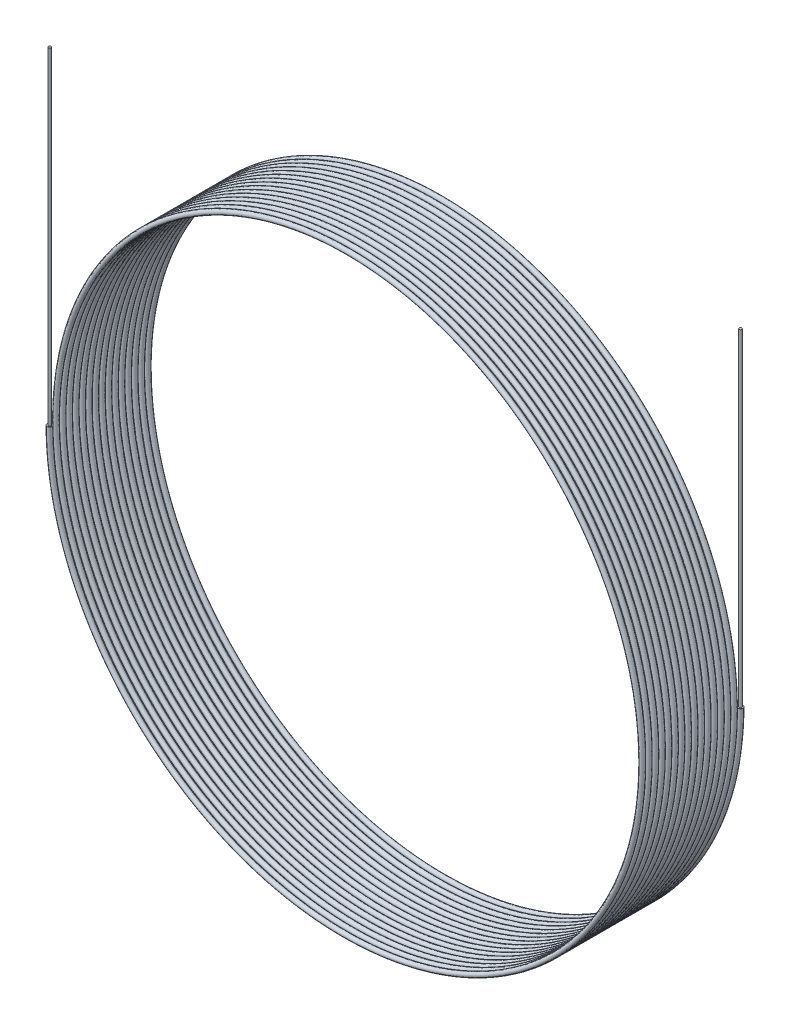
SolidWorks part; units mm, degrees
ref_plane "Front Plane" through (0, 0, 0) normal (0, 0, 1) x (1, 0, 0)
ref_plane "Top Plane" through (0, 0, 0) normal (0, 1, 0) x (1, 0, 0)
ref_plane "Right Plane" through (0, 0, 0) normal (1, 0, 0) x (0, 0, -1)
sketch "Sketch1" plane through (0, 0, 0) normal (0, 0, 1) x (1, 0, 0)
  circle A0 centre (0, 0) radius 90
  dimension "D1" = 180
curve "Helix/Spiral1" pitch 2 height 31 turns 15.5
sketch "Sketch2" plane through (0, 0, 0) normal (0, 1, 0) x (1, 0, 0)
  circle A0 centre (90, 0) radius 0.75
  spline S0 degree 3 poles (90, 0) (90, -0.0158) (89.3294, -0.0476) (86.3342, -0.0951) (81.4162, -0.1426) (74.6852, -0.1902) (66.2909, -0.2377) (56.4203, -0.2853) (45.2932, -0.3328) (33.1575, -0.3804) (20.2833, -0.4279) (6.9574, -0.4755) (-6.5234, -0.523) (-19.8589, -0.5706) (-32.7522, -0.6181) (-44.9161, -0.6656) (-56.0797, -0.7132) (-65.9944, -0.7607) (-74.4395, -0.8083) (-81.2267, -0.8558) (-86.2051, -0.9034) (-89.2636, -0.9509) (-90.3342, -0.9985) (-89.3931, -1.046) (-86.4613, -1.0936) (-81.6039, -1.1411) (-74.9292, -1.1887) (-66.5858, -1.2362) (-56.7596, -1.2837) (-45.6693, -1.3313) (-33.562, -1.3788) (-20.7072, -1.4264) (-7.3913, -1.4739) (6.0892, -1.5215) (19.4341, -1.569) (32.3462, -1.6166) (44.5379, -1.6641) (55.7378, -1.7117) (65.6964, -1.7592) (74.192, -1.8067) (81.0353, -1.8543) (86.0739, -1.9018) (89.1957, -1.9494) (90.3311, -1.9969) (89.4548, -2.0445) (86.5864, -2.092) (81.7896, -2.1396) (75.1715, -2.1871) (66.8792, -2.2347) (57.0976, -2.2822) (46.0443, -2.3298) (33.9657, -2.3773) (21.1307, -2.4248) (7.8251, -2.4724) (-5.6548, -2.5199) (-19.0088, -2.5675) (-31.9394, -2.615) (-44.1587, -2.6626) (-55.3946, -2.7101) (-65.3969, -2.7577) (-73.9428, -2.8052) (-80.842, -2.8528) (-85.9408, -2.9003) (-89.1258, -2.9479) (-90.3259, -2.9954) (-89.5144, -3.0429) (-86.7095, -3.0905) (-81.9735, -3.138) (-75.412, -3.1856) (-67.171, -3.2331) (-57.4342, -3.2807) (-46.4183, -3.3282) (-34.3687, -3.3758) (-21.5536, -3.4233) (-8.2586, -3.4709) (5.2203, -3.5184) (18.583, -3.566) (31.5319, -3.6135) (43.7785, -3.661) (55.0502, -3.7086) (65.0959, -3.7561) (73.6919, -3.8037) (80.6468, -3.8512) (85.8057, -3.8988) (89.0537, -3.9463) (90.3185, -3.9939) (89.5719, -4.0414) (86.8305, -4.089) (82.1554, -4.1365) (75.6507, -4.184) (67.4613, -4.2316) (57.7695, -4.2791) (46.7912, -4.3267) (34.7708, -4.3742) (21.9761, -4.4218) (8.692, -4.4693) (-4.7857, -4.5169) (-18.1569, -4.5644) (-31.1236, -4.612) (-43.3973, -4.6595) (-54.7044, -4.7071) (-64.7933, -4.7546) (-73.4393, -4.8021) (-80.4498, -4.8497) (-85.6686, -4.8972) (-88.9796, -4.9448) (-90.3091, -4.9923) (-89.6273, -5.0399) (-86.9496, -5.0874) (-82.3355, -5.135) (-75.8877, -5.1825) (-67.75, -5.2301) (-58.1034, -5.2776) (-47.1629, -5.3252) (-35.1721, -5.3727) (-22.398, -5.4202) (-9.1251, -5.4678) (4.351, -5.5153) (17.7303, -5.5629) (30.7146, -5.6104) (43.015, -5.658) (54.3574, -5.7055) (64.4893, -5.7531) (73.185, -5.8006) (80.2509, -5.8482) (85.5295, -5.8957) (88.9035, -5.9433) (90.2975, -5.9908) (89.6807, -6.0383) (87.0666, -6.0859) (82.5136, -6.1334) (76.123, -6.181) (68.0371, -6.2285) (58.4361, -6.2761) (47.5336, -6.3236) (35.5726, -6.3712) (22.8194, -6.4187) (9.558, -6.4663) (-3.9162, -6.5138) (-17.3032, -6.5613) (-30.3049, -6.6089) (-42.6317, -6.6564) (-54.0091, -6.704) (-64.1837, -6.7515) (-72.929, -6.7991) (-80.0501, -6.8466) (-85.3885, -6.8942) (-88.8253, -6.9417) (-90.2839, -6.9893) (-89.7319, -7.0368) (-87.1816, -7.0844) (-82.6898, -7.1319) (-76.3565, -7.1794) (-68.3227, -7.227) (-58.7673, -7.2745) (-47.9032, -7.3221) (-35.9723, -7.3696) (-23.2403, -7.4172) (-9.9908, -7.4647) (3.4813, -7.5123) (16.8758, -7.5598) (29.8945, -7.6074) (42.2475, -7.6549) (53.6596, -7.7025) (63.8767, -7.75) (72.6713, -7.7975) (79.8474, -7.8451) (85.2454, -7.8926) (88.745, -7.9402) (90.2682, -7.9877) (89.7811, -8.0353) (87.2946, -8.0828) (82.8641, -8.1304) (76.5882, -8.1779) (68.6066, -8.2255) (59.0972, -8.273) (48.2717, -8.3206) (36.3712, -8.3681) (23.6607, -8.4156) (10.4232, -8.4632) (-3.0463, -8.5107) (-16.448, -8.5583) (-29.4834, -8.6058) (-41.8623, -8.6534) (-53.3088, -8.7009) (-63.5682, -8.7485) (-72.4119, -8.796) (-79.643, -8.8436) (-85.1004, -8.8911) (-88.6626, -8.9387) (-90.2504, -8.9862) (-89.8282, -9.0337) (-87.4056, -9.0813) (-83.0365, -9.1288) (-76.8181, -9.1764) (-68.889, -9.2239) (-59.4257, -9.2715) (-48.639, -9.319) (-36.7692, -9.3666) (-24.0805, -9.4141) (-10.8555, -9.4617) (2.6113, -9.5092) (16.0198, -9.5567) (29.0717, -9.6043) (41.4761, -9.6518) (52.9568, -9.6994) (63.2582, -9.7469) (72.1508, -9.7945) (79.4366, -9.842) (84.9534, -9.8896) (88.5782, -9.9371) (90.2304, -9.9847) (89.8732, -10.0322) (87.5145, -10.0798) (83.2069, -10.1273) (77.0462, -10.1748) (69.1698, -10.2224) (59.7529, -10.2699) (49.0053, -10.3175) (37.1663, -10.365) (24.4997, -10.4126) (11.2875, -10.4601) (-2.1761, -10.5077) (-15.5913, -10.5552) (-28.6592, -10.6028) (-41.0889, -10.6503) (-52.6036, -10.6979) (-62.9467, -10.7454) (-71.888, -10.7929) (-79.2284, -10.8405) (-84.8044, -10.888) (-88.4918, -10.9356) (-90.2084, -10.9831) (-89.9162, -11.0307) (-87.6214, -11.0782) (-83.3754, -11.1258) (-77.2726, -11.1733) (-69.4489, -11.2209) (-60.0786, -11.2684) (-49.3704, -11.316) (-37.5626, -11.3635) (-24.9184, -11.411) (-11.7192, -11.4586) (1.741, -11.5061) (15.1624, -11.5537) (28.2461, -11.6012) (40.7008, -11.6488) (52.2491, -11.6963) (62.6338, -11.7439) (71.6236, -11.7914) (79.0184, -11.839) (84.6534, -11.8865) (88.4033, -11.934) (90.1843, -11.9816) (89.957, -12.0291) (87.7263, -12.0767) (83.542, -12.1242) (77.4971, -12.1718) (69.7265, -12.2193) (60.403, -12.2669) (49.7343, -12.3144) (37.958, -12.362) (25.3365, -12.4095) (12.1506, -12.4571) (-1.3058, -12.5046) (-14.7331, -12.5521) (-27.8323, -12.5997) (-40.3117, -12.6472) (-51.8934, -12.6948) (-62.3194, -12.7423) (-71.3575, -12.7899) (-78.8065, -12.8374) (-84.5005, -12.885) (-88.3127, -12.9325) (-90.1581, -12.9801) (-89.9957, -13.0276) (-87.8292, -13.0752) (-83.7066, -13.1227) (-77.7199, -13.1702) (-70.0024, -13.2178) (-60.7259, -13.2653) (-50.0971, -13.3129) (-38.3526, -13.3604) (-25.754, -13.408) (-12.5818, -13.4555) (0.8705, -13.5031) (14.3035, -13.5506) (27.4179, -13.5982) (39.9217, -13.6457) (51.5365, -13.6933) (62.0036, -13.7408) (71.0898, -13.7883) (78.5929, -13.8359) (84.3457, -13.8834) (88.2201, -13.931) (90.1298, -13.9785) (90.0324, -14.0261) (87.9299, -14.0736) (83.8693, -14.1212) (77.9409, -14.1687) (70.2767, -14.2163) (61.0475, -14.2638) (50.4587, -14.3113) (38.7462, -14.3589) (26.1709, -14.4064) (13.0127, -14.454) (-0.4353, -14.5015) (-13.8735, -14.5491) (-27.0029, -14.5966) (-39.5308, -14.6442) (-51.1784, -14.6917) (-61.6863, -14.7393) (-70.8204, -14.7868) (-78.3773, -14.8344) (-84.1888, -14.8819) (-88.1254, -14.9294) (-90.0995, -14.977) (-90.067, -15.0245) (-88.0287, -15.0721) (-84.03, -15.1196) (-78.16, -15.1672) (-70.5494, -15.2147) (-61.3676, -15.2623) (-50.8192, -15.3098) (-39.139, -15.3574) (-26.5872, -15.4049) (-9.062, -15.4683) (9.062, -15.5317) (26.5872, -15.5951) (39.139, -15.6426) (50.8192, -15.6902) (61.3676, -15.7377) (70.5494, -15.7853) (78.16, -15.8328) (84.03, -15.8804) (88.0287, -15.9279) (90.067, -15.9755) (90.0995, -16.023) (88.1254, -16.0706) (84.1888, -16.1181) (78.3773, -16.1656) (70.8204, -16.2132) (61.6863, -16.2607) (51.1784, -16.3083) (39.5308, -16.3558) (27.0029, -16.4034) (13.8735, -16.4509) (0.4353, -16.4985) (-13.0127, -16.546) (-26.1709, -16.5936) (-38.7462, -16.6411) (-50.4587, -16.6887) (-61.0475, -16.7362) (-70.2767, -16.7837) (-77.9409, -16.8313) (-83.8693, -16.8788) (-87.9299, -16.9264) (-90.0324, -16.9739) (-90.1298, -17.0215) (-88.2201, -17.069) (-84.3457, -17.1166) (-78.5929, -17.1641) (-71.0898, -17.2117) (-62.0036, -17.2592) (-51.5365, -17.3067) (-39.9217, -17.3543) (-27.4179, -17.4018) (-14.3035, -17.4494) (-0.8705, -17.4969) (12.5818, -17.5445) (25.754, -17.592) (38.3526, -17.6396) (50.0971, -17.6871) (60.7259, -17.7347) (70.0024, -17.7822) (77.7199, -17.8298) (83.7066, -17.8773) (87.8292, -17.9248) (89.9957, -17.9724) (90.1581, -18.0199) (88.3127, -18.0675) (84.5005, -18.115) (78.8065, -18.1626) (71.3575, -18.2101) (62.3194, -18.2577) (51.8934, -18.3052) (40.3117, -18.3528) (27.8323, -18.4003) (14.7331, -18.4479) (1.3058, -18.4954) (-12.1506, -18.5429) (-25.3365, -18.5905) (-37.958, -18.638) (-49.7343, -18.6856) (-60.403, -18.7331) (-69.7265, -18.7807) (-77.4971, -18.8282) (-83.542, -18.8758) (-87.7263, -18.9233) (-89.957, -18.9709) (-90.1843, -19.0184) (-88.4033, -19.066) (-84.6534, -19.1135) (-79.0184, -19.161) (-71.6236, -19.2086) (-62.6338, -19.2561) (-52.2491, -19.3037) (-40.7008, -19.3512) (-28.2461, -19.3988) (-15.1624, -19.4463) (-1.741, -19.4939) (11.7192, -19.5414) (24.9184, -19.589) (37.5626, -19.6365) (49.3704, -19.684) (60.0786, -19.7316) (69.4489, -19.7791) (77.2726, -19.8267) (83.3754, -19.8742) (87.6214, -19.9218) (89.9162, -19.9693) (90.2084, -20.0169) (88.4918, -20.0644) (84.8044, -20.112) (79.2284, -20.1595) (71.888, -20.2071) (62.9467, -20.2546) (52.6036, -20.3021) (41.0889, -20.3497) (28.6592, -20.3972) (15.5913, -20.4448) (2.1761, -20.4923) (-11.2875, -20.5399) (-24.4997, -20.5874) (-37.1663, -20.635) (-49.0053, -20.6825) (-59.7529, -20.7301) (-69.1698, -20.7776) (-77.0462, -20.8252) (-83.2069, -20.8727) (-87.5145, -20.9202) (-89.8732, -20.9678) (-90.2304, -21.0153) (-88.5782, -21.0629) (-84.9534, -21.1104) (-79.4366, -21.158) (-72.1508, -21.2055) (-63.2582, -21.2531) (-52.9568, -21.3006) (-41.4761, -21.3482) (-29.0717, -21.3957) (-16.0198, -21.4433) (-2.6113, -21.4908) (10.8555, -21.5383) (24.0805, -21.5859) (36.7692, -21.6334) (48.639, -21.681) (59.4257, -21.7285) (68.889, -21.7761) (76.8181, -21.8236) (83.0365, -21.8712) (87.4056, -21.9187) (89.8282, -21.9663) (90.2504, -22.0138) (88.6626, -22.0613) (85.1004, -22.1089) (79.643, -22.1564) (72.4119, -22.204) (63.5682, -22.2515) (53.3088, -22.2991) (41.8623, -22.3466) (29.4834, -22.3942) (16.448, -22.4417) (3.0463, -22.4893) (-10.4232, -22.5368) (-23.6607, -22.5844) (-36.3712, -22.6319) (-48.2717, -22.6794) (-59.0972, -22.727) (-68.6066, -22.7745) (-76.5882, -22.8221) (-82.8641, -22.8696) (-87.2946, -22.9172) (-89.7811, -22.9647) (-90.2682, -23.0123) (-88.745, -23.0598) (-85.2454, -23.1074) (-79.8474, -23.1549) (-72.6713, -23.2025) (-63.8767, -23.25) (-53.6596, -23.2975) (-42.2475, -23.3451) (-29.8945, -23.3926) (-16.8758, -23.4402) (-3.4813, -23.4877) (9.9908, -23.5353) (23.2403, -23.5828) (35.9723, -23.6304) (47.9032, -23.6779) (58.7673, -23.7255) (68.3227, -23.773) (76.3565, -23.8206) (82.6898, -23.8681) (87.1816, -23.9156) (89.7319, -23.9632) (90.2839, -24.0107) (88.8253, -24.0583) (85.3885, -24.1058) (80.0501, -24.1534) (72.929, -24.2009) (64.1837, -24.2485) (54.0091, -24.296) (42.6317, -24.3436) (30.3049, -24.3911) (17.3032, -24.4387) (3.9162, -24.4862) (-9.558, -24.5337) (-22.8194, -24.5813) (-35.5726, -24.6288) (-47.5336, -24.6764) (-58.4361, -24.7239) (-68.0371, -24.7715) (-76.123, -24.819) (-82.5136, -24.8666) (-87.0666, -24.9141) (-89.6807, -24.9617) (-90.2975, -25.0092) (-88.9035, -25.0567) (-85.5295, -25.1043) (-80.2509, -25.1518) (-73.185, -25.1994) (-64.4893, -25.2469) (-54.3574, -25.2945) (-43.015, -25.342) (-30.7146, -25.3896) (-17.7303, -25.4371) (-4.351, -25.4847) (9.1251, -25.5322) (22.398, -25.5798) (35.1721, -25.6273) (47.1629, -25.6748) (58.1034, -25.7224) (67.75, -25.7699) (75.8877, -25.8175) (82.3355, -25.865) (86.9496, -25.9126) (89.6273, -25.9601) (90.3091, -26.0077) (88.9796, -26.0552) (85.6686, -26.1028) (80.4498, -26.1503) (73.4393, -26.1979) (64.7933, -26.2454) (54.7044, -26.2929) (43.3973, -26.3405) (31.1236, -26.388) (18.1569, -26.4356) (4.7857, -26.4831) (-8.692, -26.5307) (-21.9761, -26.5782) (-34.7708, -26.6258) (-46.7912, -26.6733) (-57.7695, -26.7209) (-67.4613, -26.7684) (-75.6507, -26.816) (-82.1554, -26.8635) (-86.8305, -26.911) (-89.5719, -26.9586) (-90.3185, -27.0061) (-89.0537, -27.0537) (-85.8057, -27.1012) (-80.6468, -27.1488) (-73.6919, -27.1963) (-65.0959, -27.2439) (-55.0502, -27.2914) (-43.7785, -27.339) (-31.5319, -27.3865) (-18.583, -27.434) (-5.2203, -27.4816) (8.2586, -27.5291) (21.5536, -27.5767) (34.3687, -27.6242) (46.4183, -27.6718) (57.4342, -27.7193) (67.171, -27.7669) (75.412, -27.8144) (81.9735, -27.862) (86.7095, -27.9095) (89.5144, -27.9571) (90.3259, -28.0046) (89.1258, -28.0521) (85.9408, -28.0997) (80.842, -28.1472) (73.9428, -28.1948) (65.3969, -28.2423) (55.3946, -28.2899) (44.1587, -28.3374) (31.9394, -28.385) (19.0088, -28.4325) (5.6548, -28.4801) (-7.8251, -28.5276) (-21.1307, -28.5752) (-33.9657, -28.6227) (-46.0443, -28.6702) (-57.0976, -28.7178) (-66.8792, -28.7653) (-75.1715, -28.8129) (-81.7896, -28.8604) (-86.5864, -28.908) (-89.4548, -28.9555) (-90.3311, -29.0031) (-89.1957, -29.0506) (-86.0739, -29.0982) (-81.0353, -29.1457) (-74.192, -29.1933) (-65.6964, -29.2408) (-55.7378, -29.2883) (-44.5379, -29.3359) (-32.3462, -29.3834) (-19.4341, -29.431) (-6.0892, -29.4785) (7.3913, -29.5261) (20.7072, -29.5736) (33.562, -29.6212) (45.6693, -29.6687) (56.7596, -29.7163) (66.5858, -29.7638) (74.9292, -29.8113) (81.6039, -29.8589) (86.4613, -29.9064) (89.3931, -29.954) (90.3342, -30.0015) (89.2636, -30.0491) (86.2051, -30.0966) (81.2267, -30.1442) (74.4395, -30.1917) (65.9944, -30.2393) (56.0797, -30.2868) (44.9161, -30.3344) (32.7522, -30.3819) (19.8589, -30.4294) (6.5234, -30.477) (-6.9574, -30.5245) (-20.2833, -30.5721) (-33.1575, -30.6196) (-45.2932, -30.6672) (-56.4203, -30.7147) (-66.2909, -30.7623) (-74.6852, -30.8098) (-81.4162, -30.8574) (-86.3342, -30.9049) (-89.3294, -30.9524) (-90, -30.9842) (-90, -31) knots 0 0 0 0 0.001534 0.003067 0.004601 0.006135 0.007669 0.009202 0.010736 0.01227 0.013804 0.015337 0.016871 0.018405 0.019939 0.021472 0.023006 0.02454 0.026074 0.027607 0.029141 0.030675 0.032209 0.033742 0.035276 0.03681 0.038344 0.039877 0.041411 0.042945 0.044479 0.046012 0.047546 0.04908 0.050613 0.052147 0.053681 0.055215 0.056748 0.058282 0.059816 0.06135 0.062883 0.064417 0.065951 0.067485 0.069018 0.070552 0.072086 0.07362 0.075153 0.076687 0.078221 0.079755 0.081288 0.082822 0.084356 0.08589 0.087423 0.088957 0.090491 0.092025 0.093558 0.095092 0.096626 0.09816 0.099693 0.101227 0.102761 0.104294 0.105828 0.107362 0.108896 0.110429 0.111963 0.113497 0.115031 0.116564 0.118098 0.119632 0.121166 0.122699 0.124233 0.125767 0.127301 0.128834 0.130368 0.131902 0.133436 0.134969 0.136503 0.138037 0.139571 0.141104 0.142638 0.144172 0.145706 0.147239 0.148773 0.150307 0.15184 0.153374 0.154908 0.156442 0.157975 0.159509 0.161043 0.162577 0.16411 0.165644 0.167178 0.168712 0.170245 0.171779 0.173313 0.174847 0.17638 0.177914 0.179448 0.180982 0.182515 0.184049 0.185583 0.187117 0.18865 0.190184 0.191718 0.193252 0.194785 0.196319 0.197853 0.199387 0.20092 0.202454 0.203988 0.205521 0.207055 0.208589 0.210123 0.211656 0.21319 0.214724 0.216258 0.217791 0.219325 0.220859 0.222393 0.223926 0.22546 0.226994 0.228528 0.230061 0.231595 0.233129 0.234663 0.236196 0.23773 0.239264 0.240798 0.242331 0.243865 0.245399 0.246933 0.248466 0.25 0.251534 0.253067 0.254601 0.256135 0.257669 0.259202 0.260736 0.26227 0.263804 0.265337 0.266871 0.268405 0.269939 0.271472 0.273006 0.27454 0.276074 0.277607 0.279141 0.280675 0.282209 0.283742 0.285276 0.28681 0.288344 0.289877 0.291411 0.292945 0.294479 0.296012 0.297546 0.29908 0.300613 0.302147 0.303681 0.305215 0.306748 0.308282 0.309816 0.31135 0.312883 0.314417 0.315951 0.317485 0.319018 0.320552 0.322086 0.32362 0.325153 0.326687 0.328221 0.329755 0.331288 0.332822 0.334356 0.33589 0.337423 0.338957 0.340491 0.342025 0.343558 0.345092 0.346626 0.34816 0.349693 0.351227 0.352761 0.354294 0.355828 0.357362 0.358896 0.360429 0.361963 0.363497 0.365031 0.366564 0.368098 0.369632 0.371166 0.372699 0.374233 0.375767 0.377301 0.378834 0.380368 0.381902 0.383436 0.384969 0.386503 0.388037 0.389571 0.391104 0.392638 0.394172 0.395706 0.397239 0.398773 0.400307 0.40184 0.403374 0.404908 0.406442 0.407975 0.409509 0.411043 0.412577 0.41411 0.415644 0.417178 0.418712 0.420245 0.421779 0.423313 0.424847 0.42638 0.427914 0.429448 0.430982 0.432515 0.434049 0.435583 0.437117 0.43865 0.440184 0.441718 0.443252 0.444785 0.446319 0.447853 0.449387 0.45092 0.452454 0.453988 0.455521 0.457055 0.458589 0.460123 0.461656 0.46319 0.464724 0.466258 0.467791 0.469325 0.470859 0.472393 0.473926 0.47546 0.476994 0.478528 0.480061 0.481595 0.483129 0.484663 0.486196 0.48773 0.489264 0.490798 0.492331 0.493865 0.495399 0.496933 0.498466 0.501534 0.503067 0.504601 0.506135 0.507669 0.509202 0.510736 0.51227 0.513804 0.515337 0.516871 0.518405 0.519939 0.521472 0.523006 0.52454 0.526074 0.527607 0.529141 0.530675 0.532209 0.533742 0.535276 0.53681 0.538344 0.539877 0.541411 0.542945 0.544479 0.546012 0.547546 0.54908 0.550613 0.552147 0.553681 0.555215 0.556748 0.558282 0.559816 0.56135 0.562883 0.564417 0.565951 0.567485 0.569018 0.570552 0.572086 0.57362 0.575153 0.576687 0.578221 0.579755 0.581288 0.582822 0.584356 0.58589 0.587423 0.588957 0.590491 0.592025 0.593558 0.595092 0.596626 0.59816 0.599693 0.601227 0.602761 0.604294 0.605828 0.607362 0.608896 0.610429 0.611963 0.613497 0.615031 0.616564 0.618098 0.619632 0.621166 0.622699 0.624233 0.625767 0.627301 0.628834 0.630368 0.631902 0.633436 0.634969 0.636503 0.638037 0.639571 0.641104 0.642638 0.644172 0.645706 0.647239 0.648773 0.650307 0.65184 0.653374 0.654908 0.656442 0.657975 0.659509 0.661043 0.662577 0.66411 0.665644 0.667178 0.668712 0.670245 0.671779 0.673313 0.674847 0.67638 0.677914 0.679448 0.680982 0.682515 0.684049 0.685583 0.687117 0.68865 0.690184 0.691718 0.693252 0.694785 0.696319 0.697853 0.699387 0.70092 0.702454 0.703988 0.705521 0.707055 0.708589 0.710123 0.711656 0.71319 0.714724 0.716258 0.717791 0.719325 0.720859 0.722393 0.723926 0.72546 0.726994 0.728528 0.730061 0.731595 0.733129 0.734663 0.736196 0.73773 0.739264 0.740798 0.742331 0.743865 0.745399 0.746933 0.748466 0.75 0.751534 0.753067 0.754601 0.756135 0.757669 0.759202 0.760736 0.76227 0.763804 0.765337 0.766871 0.768405 0.769939 0.771472 0.773006 0.77454 0.776074 0.777607 0.779141 0.780675 0.782209 0.783742 0.785276 0.78681 0.788344 0.789877 0.791411 0.792945 0.794479 0.796012 0.797546 0.79908 0.800613 0.802147 0.803681 0.805215 0.806748 0.808282 0.809816 0.81135 0.812883 0.814417 0.815951 0.817485 0.819018 0.820552 0.822086 0.82362 0.825153 0.826687 0.828221 0.829755 0.831288 0.832822 0.834356 0.83589 0.837423 0.838957 0.840491 0.842025 0.843558 0.845092 0.846626 0.84816 0.849693 0.851227 0.852761 0.854294 0.855828 0.857362 0.858896 0.860429 0.861963 0.863497 0.865031 0.866564 0.868098 0.869632 0.871166 0.872699 0.874233 0.875767 0.877301 0.878834 0.880368 0.881902 0.883436 0.884969 0.886503 0.888037 0.889571 0.891104 0.892638 0.894172 0.895706 0.897239 0.898773 0.900307 0.90184 0.903374 0.904908 0.906442 0.907975 0.909509 0.911043 0.912577 0.91411 0.915644 0.917178 0.918712 0.920245 0.921779 0.923313 0.924847 0.92638 0.927914 0.929448 0.930982 0.932515 0.934049 0.935583 0.937117 0.93865 0.940184 0.941718 0.943252 0.944785 0.946319 0.947853 0.949387 0.95092 0.952454 0.953988 0.955521 0.957055 0.958589 0.960123 0.961656 0.96319 0.964724 0.966258 0.967791 0.969325 0.970859 0.972393 0.973926 0.97546 0.976994 0.978528 0.980061 0.981595 0.983129 0.984663 0.986196 0.98773 0.989264 0.990798 0.992331 0.993865 0.995399 0.996933 0.998466 1 1 1 1 construction
  dimension "D1" = 1.5
sweep "Sweep1" add profiles "Sketch2" path "Helix/Spiral1"
sketch "Sketch3" plane through (0, 0, 0) normal (0, 1, 0) x (1, 0, 0)
  circle A0 centre (90, 0) radius 0.4
  circle A1 centre (-89.9487, -30.9893) radius 0.4
  spline S0 degree 3 poles (90, 0) (90, -0.0158) (89.3294, -0.0476) (86.3342, -0.0951) (81.4162, -0.1426) (74.6852, -0.1902) (66.2909, -0.2377) (56.4203, -0.2853) (45.2932, -0.3328) (33.1575, -0.3804) (20.2833, -0.4279) (6.9574, -0.4755) (-6.5234, -0.523) (-19.8589, -0.5706) (-32.7522, -0.6181) (-44.9161, -0.6656) (-56.0797, -0.7132) (-65.9944, -0.7607) (-74.4395, -0.8083) (-81.2267, -0.8558) (-86.2051, -0.9034) (-89.2636, -0.9509) (-90.3342, -0.9985) (-89.3931, -1.046) (-86.4613, -1.0936) (-81.6039, -1.1411) (-74.9292, -1.1887) (-66.5858, -1.2362) (-56.7596, -1.2837) (-45.6693, -1.3313) (-33.562, -1.3788) (-20.7072, -1.4264) (-7.3913, -1.4739) (6.0892, -1.5215) (19.4341, -1.569) (32.3462, -1.6166) (44.5379, -1.6641) (55.7378, -1.7117) (65.6964, -1.7592) (74.192, -1.8067) (81.0353, -1.8543) (86.0739, -1.9018) (89.1957, -1.9494) (90.3311, -1.9969) (89.4548, -2.0445) (86.5864, -2.092) (81.7896, -2.1396) (75.1715, -2.1871) (66.8792, -2.2347) (57.0976, -2.2822) (46.0443, -2.3298) (33.9657, -2.3773) (21.1307, -2.4248) (7.8251, -2.4724) (-5.6548, -2.5199) (-19.0088, -2.5675) (-31.9394, -2.615) (-44.1587, -2.6626) (-55.3946, -2.7101) (-65.3969, -2.7577) (-73.9428, -2.8052) (-80.842, -2.8528) (-85.9408, -2.9003) (-89.1258, -2.9479) (-90.3259, -2.9954) (-89.5144, -3.0429) (-86.7095, -3.0905) (-81.9735, -3.138) (-75.412, -3.1856) (-67.171, -3.2331) (-57.4342, -3.2807) (-46.4183, -3.3282) (-34.3687, -3.3758) (-21.5536, -3.4233) (-8.2586, -3.4709) (5.2203, -3.5184) (18.583, -3.566) (31.5319, -3.6135) (43.7785, -3.661) (55.0502, -3.7086) (65.0959, -3.7561) (73.6919, -3.8037) (80.6468, -3.8512) (85.8057, -3.8988) (89.0537, -3.9463) (90.3185, -3.9939) (89.5719, -4.0414) (86.8305, -4.089) (82.1554, -4.1365) (75.6507, -4.184) (67.4613, -4.2316) (57.7695, -4.2791) (46.7912, -4.3267) (34.7708, -4.3742) (21.9761, -4.4218) (8.692, -4.4693) (-4.7857, -4.5169) (-18.1569, -4.5644) (-31.1236, -4.612) (-43.3973, -4.6595) (-54.7044, -4.7071) (-64.7933, -4.7546) (-73.4393, -4.8021) (-80.4498, -4.8497) (-85.6686, -4.8972) (-88.9796, -4.9448) (-90.3091, -4.9923) (-89.6273, -5.0399) (-86.9496, -5.0874) (-82.3355, -5.135) (-75.8877, -5.1825) (-67.75, -5.2301) (-58.1034, -5.2776) (-47.1629, -5.3252) (-35.1721, -5.3727) (-22.398, -5.4202) (-9.1251, -5.4678) (4.351, -5.5153) (17.7303, -5.5629) (30.7146, -5.6104) (43.015, -5.658) (54.3574, -5.7055) (64.4893, -5.7531) (73.185, -5.8006) (80.2509, -5.8482) (85.5295, -5.8957) (88.9035, -5.9433) (90.2975, -5.9908) (89.6807, -6.0383) (87.0666, -6.0859) (82.5136, -6.1334) (76.123, -6.181) (68.0371, -6.2285) (58.4361, -6.2761) (47.5336, -6.3236) (35.5726, -6.3712) (22.8194, -6.4187) (9.558, -6.4663) (-3.9162, -6.5138) (-17.3032, -6.5613) (-30.3049, -6.6089) (-42.6317, -6.6564) (-54.0091, -6.704) (-64.1837, -6.7515) (-72.929, -6.7991) (-80.0501, -6.8466) (-85.3885, -6.8942) (-88.8253, -6.9417) (-90.2839, -6.9893) (-89.7319, -7.0368) (-87.1816, -7.0844) (-82.6898, -7.1319) (-76.3565, -7.1794) (-68.3227, -7.227) (-58.7673, -7.2745) (-47.9032, -7.3221) (-35.9723, -7.3696) (-23.2403, -7.4172) (-9.9908, -7.4647) (3.4813, -7.5123) (16.8758, -7.5598) (29.8945, -7.6074) (42.2475, -7.6549) (53.6596, -7.7025) (63.8767, -7.75) (72.6713, -7.7975) (79.8474, -7.8451) (85.2454, -7.8926) (88.745, -7.9402) (90.2682, -7.9877) (89.7811, -8.0353) (87.2946, -8.0828) (82.8641, -8.1304) (76.5882, -8.1779) (68.6066, -8.2255) (59.0972, -8.273) (48.2717, -8.3206) (36.3712, -8.3681) (23.6607, -8.4156) (10.4232, -8.4632) (-3.0463, -8.5107) (-16.448, -8.5583) (-29.4834, -8.6058) (-41.8623, -8.6534) (-53.3088, -8.7009) (-63.5682, -8.7485) (-72.4119, -8.796) (-79.643, -8.8436) (-85.1004, -8.8911) (-88.6626, -8.9387) (-90.2504, -8.9862) (-89.8282, -9.0337) (-87.4056, -9.0813) (-83.0365, -9.1288) (-76.8181, -9.1764) (-68.889, -9.2239) (-59.4257, -9.2715) (-48.639, -9.319) (-36.7692, -9.3666) (-24.0805, -9.4141) (-10.8555, -9.4617) (2.6113, -9.5092) (16.0198, -9.5567) (29.0717, -9.6043) (41.4761, -9.6518) (52.9568, -9.6994) (63.2582, -9.7469) (72.1508, -9.7945) (79.4366, -9.842) (84.9534, -9.8896) (88.5782, -9.9371) (90.2304, -9.9847) (89.8732, -10.0322) (87.5145, -10.0798) (83.2069, -10.1273) (77.0462, -10.1748) (69.1698, -10.2224) (59.7529, -10.2699) (49.0053, -10.3175) (37.1663, -10.365) (24.4997, -10.4126) (11.2875, -10.4601) (-2.1761, -10.5077) (-15.5913, -10.5552) (-28.6592, -10.6028) (-41.0889, -10.6503) (-52.6036, -10.6979) (-62.9467, -10.7454) (-71.888, -10.7929) (-79.2284, -10.8405) (-84.8044, -10.888) (-88.4918, -10.9356) (-90.2084, -10.9831) (-89.9162, -11.0307) (-87.6214, -11.0782) (-83.3754, -11.1258) (-77.2726, -11.1733) (-69.4489, -11.2209) (-60.0786, -11.2684) (-49.3704, -11.316) (-37.5626, -11.3635) (-24.9184, -11.411) (-11.7192, -11.4586) (1.741, -11.5061) (15.1624, -11.5537) (28.2461, -11.6012) (40.7008, -11.6488) (52.2491, -11.6963) (62.6338, -11.7439) (71.6236, -11.7914) (79.0184, -11.839) (84.6534, -11.8865) (88.4033, -11.934) (90.1843, -11.9816) (89.957, -12.0291) (87.7263, -12.0767) (83.542, -12.1242) (77.4971, -12.1718) (69.7265, -12.2193) (60.403, -12.2669) (49.7343, -12.3144) (37.958, -12.362) (25.3365, -12.4095) (12.1506, -12.4571) (-1.3058, -12.5046) (-14.7331, -12.5521) (-27.8323, -12.5997) (-40.3117, -12.6472) (-51.8934, -12.6948) (-62.3194, -12.7423) (-71.3575, -12.7899) (-78.8065, -12.8374) (-84.5005, -12.885) (-88.3127, -12.9325) (-90.1581, -12.9801) (-89.9957, -13.0276) (-87.8292, -13.0752) (-83.7066, -13.1227) (-77.7199, -13.1702) (-70.0024, -13.2178) (-60.7259, -13.2653) (-50.0971, -13.3129) (-38.3526, -13.3604) (-25.754, -13.408) (-12.5818, -13.4555) (0.8705, -13.5031) (14.3035, -13.5506) (27.4179, -13.5982) (39.9217, -13.6457) (51.5365, -13.6933) (62.0036, -13.7408) (71.0898, -13.7883) (78.5929, -13.8359) (84.3457, -13.8834) (88.2201, -13.931) (90.1298, -13.9785) (90.0324, -14.0261) (87.9299, -14.0736) (83.8693, -14.1212) (77.9409, -14.1687) (70.2767, -14.2163) (61.0475, -14.2638) (50.4587, -14.3113) (38.7462, -14.3589) (26.1709, -14.4064) (13.0127, -14.454) (-0.4353, -14.5015) (-13.8735, -14.5491) (-27.0029, -14.5966) (-39.5308, -14.6442) (-51.1784, -14.6917) (-61.6863, -14.7393) (-70.8204, -14.7868) (-78.3773, -14.8344) (-84.1888, -14.8819) (-88.1254, -14.9294) (-90.0995, -14.977) (-90.067, -15.0245) (-88.0287, -15.0721) (-84.03, -15.1196) (-78.16, -15.1672) (-70.5494, -15.2147) (-61.3676, -15.2623) (-50.8192, -15.3098) (-39.139, -15.3574) (-26.5872, -15.4049) (-9.062, -15.4683) (9.062, -15.5317) (26.5872, -15.5951) (39.139, -15.6426) (50.8192, -15.6902) (61.3676, -15.7377) (70.5494, -15.7853) (78.16, -15.8328) (84.03, -15.8804) (88.0287, -15.9279) (90.067, -15.9755) (90.0995, -16.023) (88.1254, -16.0706) (84.1888, -16.1181) (78.3773, -16.1656) (70.8204, -16.2132) (61.6863, -16.2607) (51.1784, -16.3083) (39.5308, -16.3558) (27.0029, -16.4034) (13.8735, -16.4509) (0.4353, -16.4985) (-13.0127, -16.546) (-26.1709, -16.5936) (-38.7462, -16.6411) (-50.4587, -16.6887) (-61.0475, -16.7362) (-70.2767, -16.7837) (-77.9409, -16.8313) (-83.8693, -16.8788) (-87.9299, -16.9264) (-90.0324, -16.9739) (-90.1298, -17.0215) (-88.2201, -17.069) (-84.3457, -17.1166) (-78.5929, -17.1641) (-71.0898, -17.2117) (-62.0036, -17.2592) (-51.5365, -17.3067) (-39.9217, -17.3543) (-27.4179, -17.4018) (-14.3035, -17.4494) (-0.8705, -17.4969) (12.5818, -17.5445) (25.754, -17.592) (38.3526, -17.6396) (50.0971, -17.6871) (60.7259, -17.7347) (70.0024, -17.7822) (77.7199, -17.8298) (83.7066, -17.8773) (87.8292, -17.9248) (89.9957, -17.9724) (90.1581, -18.0199) (88.3127, -18.0675) (84.5005, -18.115) (78.8065, -18.1626) (71.3575, -18.2101) (62.3194, -18.2577) (51.8934, -18.3052) (40.3117, -18.3528) (27.8323, -18.4003) (14.7331, -18.4479) (1.3058, -18.4954) (-12.1506, -18.5429) (-25.3365, -18.5905) (-37.958, -18.638) (-49.7343, -18.6856) (-60.403, -18.7331) (-69.7265, -18.7807) (-77.4971, -18.8282) (-83.542, -18.8758) (-87.7263, -18.9233) (-89.957, -18.9709) (-90.1843, -19.0184) (-88.4033, -19.066) (-84.6534, -19.1135) (-79.0184, -19.161) (-71.6236, -19.2086) (-62.6338, -19.2561) (-52.2491, -19.3037) (-40.7008, -19.3512) (-28.2461, -19.3988) (-15.1624, -19.4463) (-1.741, -19.4939) (11.7192, -19.5414) (24.9184, -19.589) (37.5626, -19.6365) (49.3704, -19.684) (60.0786, -19.7316) (69.4489, -19.7791) (77.2726, -19.8267) (83.3754, -19.8742) (87.6214, -19.9218) (89.9162, -19.9693) (90.2084, -20.0169) (88.4918, -20.0644) (84.8044, -20.112) (79.2284, -20.1595) (71.888, -20.2071) (62.9467, -20.2546) (52.6036, -20.3021) (41.0889, -20.3497) (28.6592, -20.3972) (15.5913, -20.4448) (2.1761, -20.4923) (-11.2875, -20.5399) (-24.4997, -20.5874) (-37.1663, -20.635) (-49.0053, -20.6825) (-59.7529, -20.7301) (-69.1698, -20.7776) (-77.0462, -20.8252) (-83.2069, -20.8727) (-87.5145, -20.9202) (-89.8732, -20.9678) (-90.2304, -21.0153) (-88.5782, -21.0629) (-84.9534, -21.1104) (-79.4366, -21.158) (-72.1508, -21.2055) (-63.2582, -21.2531) (-52.9568, -21.3006) (-41.4761, -21.3482) (-29.0717, -21.3957) (-16.0198, -21.4433) (-2.6113, -21.4908) (10.8555, -21.5383) (24.0805, -21.5859) (36.7692, -21.6334) (48.639, -21.681) (59.4257, -21.7285) (68.889, -21.7761) (76.8181, -21.8236) (83.0365, -21.8712) (87.4056, -21.9187) (89.8282, -21.9663) (90.2504, -22.0138) (88.6626, -22.0613) (85.1004, -22.1089) (79.643, -22.1564) (72.4119, -22.204) (63.5682, -22.2515) (53.3088, -22.2991) (41.8623, -22.3466) (29.4834, -22.3942) (16.448, -22.4417) (3.0463, -22.4893) (-10.4232, -22.5368) (-23.6607, -22.5844) (-36.3712, -22.6319) (-48.2717, -22.6794) (-59.0972, -22.727) (-68.6066, -22.7745) (-76.5882, -22.8221) (-82.8641, -22.8696) (-87.2946, -22.9172) (-89.7811, -22.9647) (-90.2682, -23.0123) (-88.745, -23.0598) (-85.2454, -23.1074) (-79.8474, -23.1549) (-72.6713, -23.2025) (-63.8767, -23.25) (-53.6596, -23.2975) (-42.2475, -23.3451) (-29.8945, -23.3926) (-16.8758, -23.4402) (-3.4813, -23.4877) (9.9908, -23.5353) (23.2403, -23.5828) (35.9723, -23.6304) (47.9032, -23.6779) (58.7673, -23.7255) (68.3227, -23.773) (76.3565, -23.8206) (82.6898, -23.8681) (87.1816, -23.9156) (89.7319, -23.9632) (90.2839, -24.0107) (88.8253, -24.0583) (85.3885, -24.1058) (80.0501, -24.1534) (72.929, -24.2009) (64.1837, -24.2485) (54.0091, -24.296) (42.6317, -24.3436) (30.3049, -24.3911) (17.3032, -24.4387) (3.9162, -24.4862) (-9.558, -24.5337) (-22.8194, -24.5813) (-35.5726, -24.6288) (-47.5336, -24.6764) (-58.4361, -24.7239) (-68.0371, -24.7715) (-76.123, -24.819) (-82.5136, -24.8666) (-87.0666, -24.9141) (-89.6807, -24.9617) (-90.2975, -25.0092) (-88.9035, -25.0567) (-85.5295, -25.1043) (-80.2509, -25.1518) (-73.185, -25.1994) (-64.4893, -25.2469) (-54.3574, -25.2945) (-43.015, -25.342) (-30.7146, -25.3896) (-17.7303, -25.4371) (-4.351, -25.4847) (9.1251, -25.5322) (22.398, -25.5798) (35.1721, -25.6273) (47.1629, -25.6748) (58.1034, -25.7224) (67.75, -25.7699) (75.8877, -25.8175) (82.3355, -25.865) (86.9496, -25.9126) (89.6273, -25.9601) (90.3091, -26.0077) (88.9796, -26.0552) (85.6686, -26.1028) (80.4498, -26.1503) (73.4393, -26.1979) (64.7933, -26.2454) (54.7044, -26.2929) (43.3973, -26.3405) (31.1236, -26.388) (18.1569, -26.4356) (4.7857, -26.4831) (-8.692, -26.5307) (-21.9761, -26.5782) (-34.7708, -26.6258) (-46.7912, -26.6733) (-57.7695, -26.7209) (-67.4613, -26.7684) (-75.6507, -26.816) (-82.1554, -26.8635) (-86.8305, -26.911) (-89.5719, -26.9586) (-90.3185, -27.0061) (-89.0537, -27.0537) (-85.8057, -27.1012) (-80.6468, -27.1488) (-73.6919, -27.1963) (-65.0959, -27.2439) (-55.0502, -27.2914) (-43.7785, -27.339) (-31.5319, -27.3865) (-18.583, -27.434) (-5.2203, -27.4816) (8.2586, -27.5291) (21.5536, -27.5767) (34.3687, -27.6242) (46.4183, -27.6718) (57.4342, -27.7193) (67.171, -27.7669) (75.412, -27.8144) (81.9735, -27.862) (86.7095, -27.9095) (89.5144, -27.9571) (90.3259, -28.0046) (89.1258, -28.0521) (85.9408, -28.0997) (80.842, -28.1472) (73.9428, -28.1948) (65.3969, -28.2423) (55.3946, -28.2899) (44.1587, -28.3374) (31.9394, -28.385) (19.0088, -28.4325) (5.6548, -28.4801) (-7.8251, -28.5276) (-21.1307, -28.5752) (-33.9657, -28.6227) (-46.0443, -28.6702) (-57.0976, -28.7178) (-66.8792, -28.7653) (-75.1715, -28.8129) (-81.7896, -28.8604) (-86.5864, -28.908) (-89.4548, -28.9555) (-90.3311, -29.0031) (-89.1957, -29.0506) (-86.0739, -29.0982) (-81.0353, -29.1457) (-74.192, -29.1933) (-65.6964, -29.2408) (-55.7378, -29.2883) (-44.5379, -29.3359) (-32.3462, -29.3834) (-19.4341, -29.431) (-6.0892, -29.4785) (7.3913, -29.5261) (20.7072, -29.5736) (33.562, -29.6212) (45.6693, -29.6687) (56.7596, -29.7163) (66.5858, -29.7638) (74.9292, -29.8113) (81.6039, -29.8589) (86.4613, -29.9064) (89.3931, -29.954) (90.3342, -30.0015) (89.2636, -30.0491) (86.2051, -30.0966) (81.2267, -30.1442) (74.4395, -30.1917) (65.9944, -30.2393) (56.0797, -30.2868) (44.9161, -30.3344) (32.7522, -30.3819) (19.8589, -30.4294) (6.5234, -30.477) (-6.9574, -30.5245) (-20.2833, -30.5721) (-33.1575, -30.6196) (-45.2932, -30.6672) (-56.4203, -30.7147) (-66.2909, -30.7623) (-74.6852, -30.8098) (-81.4162, -30.8574) (-86.3342, -30.9049) (-89.3294, -30.9524) (-90, -30.9842) (-90, -31) knots 0 0 0 0 0.001534 0.003067 0.004601 0.006135 0.007669 0.009202 0.010736 0.01227 0.013804 0.015337 0.016871 0.018405 0.019939 0.021472 0.023006 0.02454 0.026074 0.027607 0.029141 0.030675 0.032209 0.033742 0.035276 0.03681 0.038344 0.039877 0.041411 0.042945 0.044479 0.046012 0.047546 0.04908 0.050613 0.052147 0.053681 0.055215 0.056748 0.058282 0.059816 0.06135 0.062883 0.064417 0.065951 0.067485 0.069018 0.070552 0.072086 0.07362 0.075153 0.076687 0.078221 0.079755 0.081288 0.082822 0.084356 0.08589 0.087423 0.088957 0.090491 0.092025 0.093558 0.095092 0.096626 0.09816 0.099693 0.101227 0.102761 0.104294 0.105828 0.107362 0.108896 0.110429 0.111963 0.113497 0.115031 0.116564 0.118098 0.119632 0.121166 0.122699 0.124233 0.125767 0.127301 0.128834 0.130368 0.131902 0.133436 0.134969 0.136503 0.138037 0.139571 0.141104 0.142638 0.144172 0.145706 0.147239 0.148773 0.150307 0.15184 0.153374 0.154908 0.156442 0.157975 0.159509 0.161043 0.162577 0.16411 0.165644 0.167178 0.168712 0.170245 0.171779 0.173313 0.174847 0.17638 0.177914 0.179448 0.180982 0.182515 0.184049 0.185583 0.187117 0.18865 0.190184 0.191718 0.193252 0.194785 0.196319 0.197853 0.199387 0.20092 0.202454 0.203988 0.205521 0.207055 0.208589 0.210123 0.211656 0.21319 0.214724 0.216258 0.217791 0.219325 0.220859 0.222393 0.223926 0.22546 0.226994 0.228528 0.230061 0.231595 0.233129 0.234663 0.236196 0.23773 0.239264 0.240798 0.242331 0.243865 0.245399 0.246933 0.248466 0.25 0.251534 0.253067 0.254601 0.256135 0.257669 0.259202 0.260736 0.26227 0.263804 0.265337 0.266871 0.268405 0.269939 0.271472 0.273006 0.27454 0.276074 0.277607 0.279141 0.280675 0.282209 0.283742 0.285276 0.28681 0.288344 0.289877 0.291411 0.292945 0.294479 0.296012 0.297546 0.29908 0.300613 0.302147 0.303681 0.305215 0.306748 0.308282 0.309816 0.31135 0.312883 0.314417 0.315951 0.317485 0.319018 0.320552 0.322086 0.32362 0.325153 0.326687 0.328221 0.329755 0.331288 0.332822 0.334356 0.33589 0.337423 0.338957 0.340491 0.342025 0.343558 0.345092 0.346626 0.34816 0.349693 0.351227 0.352761 0.354294 0.355828 0.357362 0.358896 0.360429 0.361963 0.363497 0.365031 0.366564 0.368098 0.369632 0.371166 0.372699 0.374233 0.375767 0.377301 0.378834 0.380368 0.381902 0.383436 0.384969 0.386503 0.388037 0.389571 0.391104 0.392638 0.394172 0.395706 0.397239 0.398773 0.400307 0.40184 0.403374 0.404908 0.406442 0.407975 0.409509 0.411043 0.412577 0.41411 0.415644 0.417178 0.418712 0.420245 0.421779 0.423313 0.424847 0.42638 0.427914 0.429448 0.430982 0.432515 0.434049 0.435583 0.437117 0.43865 0.440184 0.441718 0.443252 0.444785 0.446319 0.447853 0.449387 0.45092 0.452454 0.453988 0.455521 0.457055 0.458589 0.460123 0.461656 0.46319 0.464724 0.466258 0.467791 0.469325 0.470859 0.472393 0.473926 0.47546 0.476994 0.478528 0.480061 0.481595 0.483129 0.484663 0.486196 0.48773 0.489264 0.490798 0.492331 0.493865 0.495399 0.496933 0.498466 0.501534 0.503067 0.504601 0.506135 0.507669 0.509202 0.510736 0.51227 0.513804 0.515337 0.516871 0.518405 0.519939 0.521472 0.523006 0.52454 0.526074 0.527607 0.529141 0.530675 0.532209 0.533742 0.535276 0.53681 0.538344 0.539877 0.541411 0.542945 0.544479 0.546012 0.547546 0.54908 0.550613 0.552147 0.553681 0.555215 0.556748 0.558282 0.559816 0.56135 0.562883 0.564417 0.565951 0.567485 0.569018 0.570552 0.572086 0.57362 0.575153 0.576687 0.578221 0.579755 0.581288 0.582822 0.584356 0.58589 0.587423 0.588957 0.590491 0.592025 0.593558 0.595092 0.596626 0.59816 0.599693 0.601227 0.602761 0.604294 0.605828 0.607362 0.608896 0.610429 0.611963 0.613497 0.615031 0.616564 0.618098 0.619632 0.621166 0.622699 0.624233 0.625767 0.627301 0.628834 0.630368 0.631902 0.633436 0.634969 0.636503 0.638037 0.639571 0.641104 0.642638 0.644172 0.645706 0.647239 0.648773 0.650307 0.65184 0.653374 0.654908 0.656442 0.657975 0.659509 0.661043 0.662577 0.66411 0.665644 0.667178 0.668712 0.670245 0.671779 0.673313 0.674847 0.67638 0.677914 0.679448 0.680982 0.682515 0.684049 0.685583 0.687117 0.68865 0.690184 0.691718 0.693252 0.694785 0.696319 0.697853 0.699387 0.70092 0.702454 0.703988 0.705521 0.707055 0.708589 0.710123 0.711656 0.71319 0.714724 0.716258 0.717791 0.719325 0.720859 0.722393 0.723926 0.72546 0.726994 0.728528 0.730061 0.731595 0.733129 0.734663 0.736196 0.73773 0.739264 0.740798 0.742331 0.743865 0.745399 0.746933 0.748466 0.75 0.751534 0.753067 0.754601 0.756135 0.757669 0.759202 0.760736 0.76227 0.763804 0.765337 0.766871 0.768405 0.769939 0.771472 0.773006 0.77454 0.776074 0.777607 0.779141 0.780675 0.782209 0.783742 0.785276 0.78681 0.788344 0.789877 0.791411 0.792945 0.794479 0.796012 0.797546 0.79908 0.800613 0.802147 0.803681 0.805215 0.806748 0.808282 0.809816 0.81135 0.812883 0.814417 0.815951 0.817485 0.819018 0.820552 0.822086 0.82362 0.825153 0.826687 0.828221 0.829755 0.831288 0.832822 0.834356 0.83589 0.837423 0.838957 0.840491 0.842025 0.843558 0.845092 0.846626 0.84816 0.849693 0.851227 0.852761 0.854294 0.855828 0.857362 0.858896 0.860429 0.861963 0.863497 0.865031 0.866564 0.868098 0.869632 0.871166 0.872699 0.874233 0.875767 0.877301 0.878834 0.880368 0.881902 0.883436 0.884969 0.886503 0.888037 0.889571 0.891104 0.892638 0.894172 0.895706 0.897239 0.898773 0.900307 0.90184 0.903374 0.904908 0.906442 0.907975 0.909509 0.911043 0.912577 0.91411 0.915644 0.917178 0.918712 0.920245 0.921779 0.923313 0.924847 0.92638 0.927914 0.929448 0.930982 0.932515 0.934049 0.935583 0.937117 0.93865 0.940184 0.941718 0.943252 0.944785 0.946319 0.947853 0.949387 0.95092 0.952454 0.953988 0.955521 0.957055 0.958589 0.960123 0.961656 0.96319 0.964724 0.966258 0.967791 0.969325 0.970859 0.972393 0.973926 0.97546 0.976994 0.978528 0.980061 0.981595 0.983129 0.984663 0.986196 0.98773 0.989264 0.990798 0.992331 0.993865 0.995399 0.996933 0.998466 1 1 1 1 construction
extrude "Boss-Extrude1" add sketch "Sketch3" along normal blind 100
